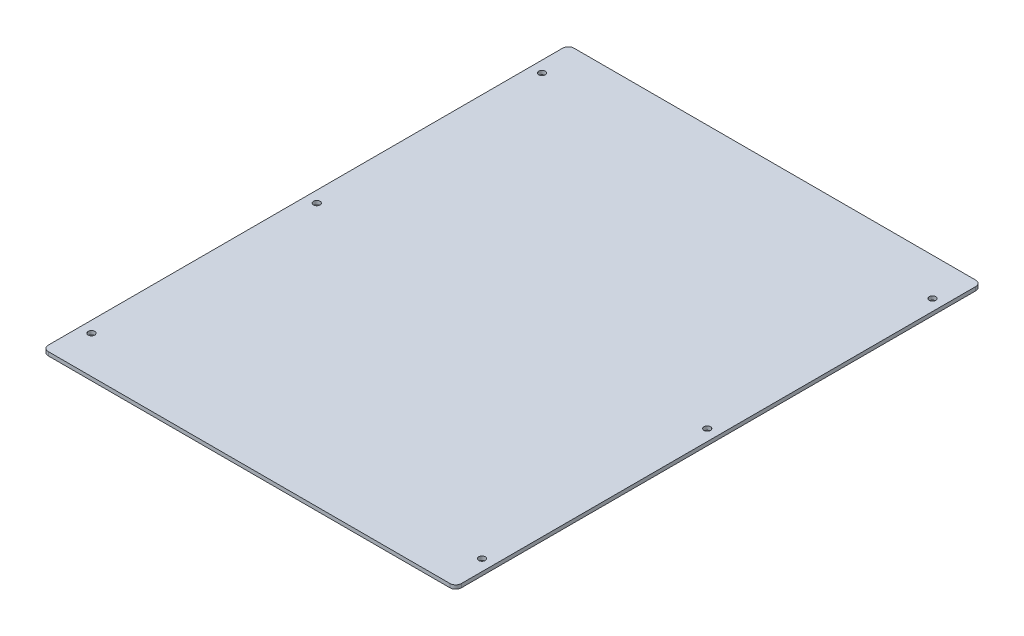
SolidWorks part; units mm, degrees
ref_plane "정면" through (0, 0, 0) normal (0, 0, 1) x (1, 0, 0)
ref_plane "윗면" through (0, 0, 0) normal (0, 1, 0) x (1, 0, 0)
ref_plane "우측면" through (0, 0, 0) normal (1, 0, 0) x (0, 0, -1)
sketch "Sketch1" plane through (0, 0, 0) normal (0, 1, 0) x (1, 0, 0)
  line L1 (-110, -140) -> (110, -140)
  line L2 (-110, -140) -> (-110, 140)
  line L3 (-110, 140) -> (110, 140)
  line L4 (110, -140) -> (110, 140)
  line L5 (-110, -140) -> (110, 140) construction
  line L6 (-110, 140) -> (110, -140) construction
  point P0 (0, 0)
  dimension "D1" = 220
  dimension "D2" = 280
extrude "Boss-Extrude1" add sketch "Sketch1" along normal blind 2
hole_wizard "Ø3.5 (3.5) Diameter Hole1" positions "Sketch3" profile "Sketch2" hole size "Ø3.5" standard "ANSI Metric" end condition through all
sketch "Sketch3" plane through (0, 2, 0) normal (0, 1, 0) x (1, 0, 0)
  line L0 (0, 164.9071) -> (0, -166.2683) construction
  line L2 (110, 140) -> (-110, 140) construction
  line L3 (-110, -140) -> (110, -140) construction
  line L4 (-153.791, 0) -> (161.9388, 0) construction
  point P0 (-104, -120)
  point P2 (104, -120)
  point P4 (104, 120)
  point P6 (-104, 120)
  point P24 (104, 0)
  point P27 (-104, 0)
  dimension "D1" = 208
  dimension "D2" = 208
  dimension "D3" = 104
  dimension "D4" = 20
  dimension "D5" = 20
sketch "Sketch2" plane through (-104, 2, 120) normal (1, 0, 0) x (0, 0, 1)
  line L0 (0, 0) -> (0, 2)
  line L1 (0, 2) -> (1.75, 2)
  line L2 (1.75, 2) -> (1.75, 0)
  line L5 (1.75, 0) -> (0, 0)
  line L11 (0, -6.35) -> (0, 107.95) construction
  dimension "Thru Hole Dia." = 3.5
  dimension "Thru Hole Depth" = 2
fillet "Fillet1" radius 3 4 edges at (-110, 1, 140) (110, 1, 140) (110, 1, -140) (-110, 1, -140)
sketch "Sketch4" plane through (0, 2, 0) normal (0, 1, 0) x (1, 0, 0)
  line L1 (-40.4443, -31.6055) -> (94.5557, -31.6055)
  line L2 (-40.4443, -31.6055) -> (-40.4443, -127.6055)
  line L3 (-40.4443, -127.6055) -> (94.5557, -127.6055)
  line L4 (94.5557, -31.6055) -> (94.5557, -127.6055)
  line L5 (-100.8537, -31.7154) -> (-49.8537, -31.7154)
  line L6 (-100.8537, -31.7154) -> (-100.8537, -108.7154)
  line L7 (-100.8537, -108.7154) -> (-49.8537, -108.7154)
  line L8 (-49.8537, -31.7154) -> (-49.8537, -108.7154)
  line L9 (-90.4961, 91.256) -> (89.5039, 91.256)
  line L10 (-90.4961, 91.256) -> (-90.4961, -3.744)
  line L11 (-90.4961, -3.744) -> (89.5039, -3.744)
  line L12 (89.5039, 91.256) -> (89.5039, -3.744)
  dimension "D1" = 135
  dimension "D2" = 96
  dimension "D3" = 51
  dimension "D4" = 77
  dimension "D5" = 180
  dimension "D6" = 95
